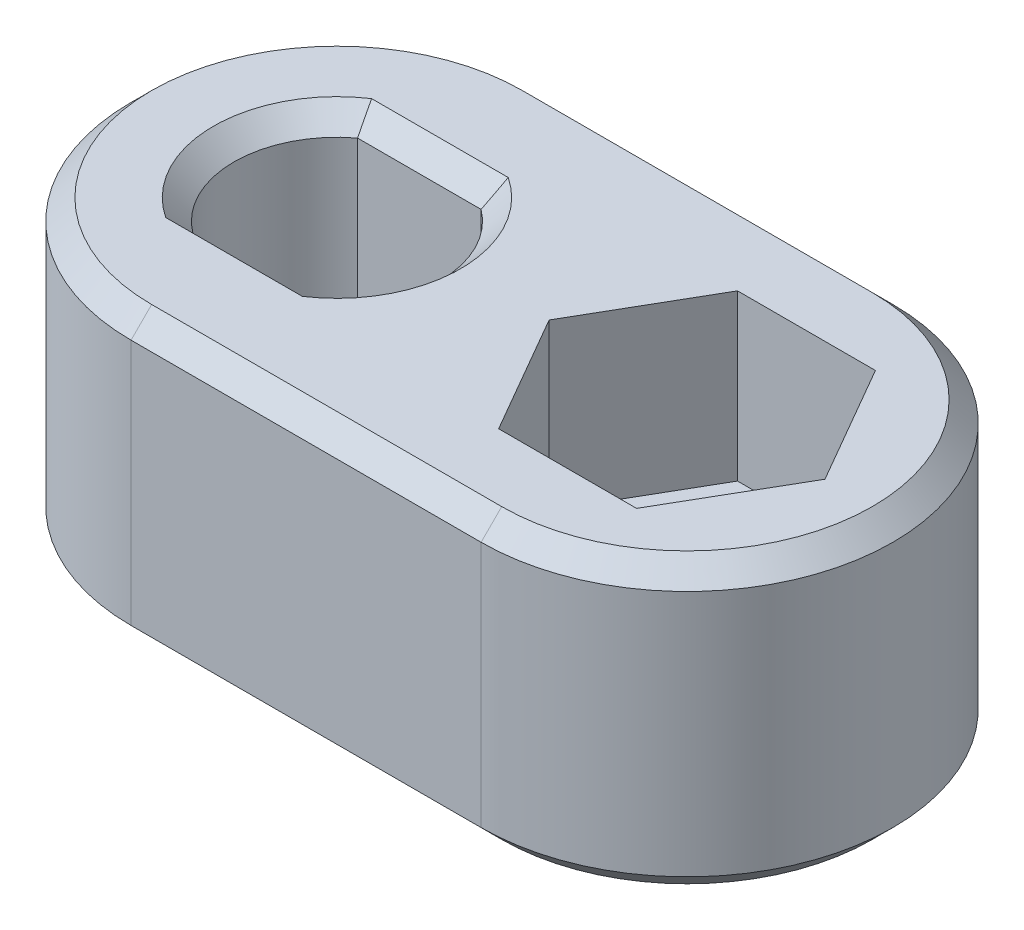
SolidWorks part; units mm, degrees
ref_plane "Front Plane" through (0, 0, 0) normal (0, 0, 1) x (1, 0, 0)
ref_plane "Top Plane" through (0, 0, 0) normal (0, 1, 0) x (1, 0, 0)
ref_plane "Right Plane" through (0, 0, 0) normal (1, 0, 0) x (0, 0, -1)
sketch "Sketch1" plane through (0, 0, 0) normal (0, 1, 0) x (1, 0, 0)
  line L0 (0, 0) -> (8.5, 0) construction
  line L1 (0, 5) -> (8.5, 5)
  line L2 (0, -5) -> (8.5, -5)
  arc A0 (0, 5) -> (0, -5) centre (0, 0) ccw
  arc A1 (8.5, -5) -> (8.5, 5) centre (8.5, 0) ccw
  point P3 (4.25, 0)
  dimension "D1" = 8.5
  dimension "D2" = 10
extrude "Boss-Extrude1" add sketch "Sketch1" along normal blind 7
sketch "Sketch2" plane through (0, 7, 0) normal (0, 1, 0) x (1, 0, 0)
  line L0 (-1.5, -2) -> (1.5, -2)
  line L1 (-1.5, 2) -> (1.5, 2)
  line L2 (0, 0) -> (-3.1448, 0) construction
  circle A0 centre (0, 0) radius 2.5
  dimension "D2" = 5
  dimension "D1" = 4
extrude "Cut-Extrude1" cut sketch "Sketch2" against normal blind 4
hole_wizard "CSK for M3 Hex Socket Countersunk Cap Screw2" positions "Sketch8" profile "Sketch7" countersink size "M3" standard "ISO"
sketch "Sketch8" plane through (0, 0, 0) normal (0, -1, 0) x (-1, 0, 0)
  point P0 (0, 0)
sketch "Sketch7" plane through (0, 0, 0) normal (1, 0, 0) x (0, 0, -1)
  line L0 (0, 0) -> (0, 8.5215)
  line L1 (0, 8.5215) -> (1.7, 7.5)
  line L2 (1.7, 7.5) -> (1.7, 1.66)
  line L3 (1.7, 1.66) -> (3.36, 0)
  line L5 (3.36, 0) -> (0, 0)
  line L6 (-1.7, 1.66) -> (-3.36, 0) construction
  line L10 (0, 8.5215) -> (-1.7, 7.5) construction
  line L11 (0, -6.35) -> (0, 107.95) construction
  dimension "Hole Dia." = 3.4
  dimension "Hole Depth" = 7.5
  dimension "Near C'Sink Dia." = 6.72
  dimension "Near C'Sink Angle" = 90
  dimension "Drill Angle" = 118
hole_wizard "Hole1" positions "Sketch9" profile "Sketch10" legacy end condition through all
sketch "Sketch9" plane through (0, 0, 0) normal (0, -1, 0) x (-1, 0, 0)
  point P0 (-8.5, 0)
sketch "Sketch10" plane through (8.5, 0, 0) normal (1, 0, 0) x (0, 0, -1)
  line L0 (0, 0) -> (0, 7)
  line L1 (0, 7) -> (2.075, 7)
  line L2 (2.075, 7) -> (2.075, 0)
  line L3 (2.075, 0) -> (0, 0)
  line L4 (0, 110) -> (0, -10) construction
  dimension "Diameter" = 4.15
  dimension "Depth" = 7
sketch "Sketch11" plane through (0, 7, 0) normal (0, 1, 0) x (1, 0, 0)
  line L0 (8.5, 5) -> (0, 5) construction
  line L1 (11.8486, 0) -> (10.1743, 2.9)
  line L2 (10.1743, 2.9) -> (6.8257, 2.9)
  line L3 (6.8257, 2.9) -> (5.1514, 0)
  line L4 (5.1514, 0) -> (6.8257, -2.9)
  line L5 (6.8257, -2.9) -> (10.1743, -2.9)
  line L6 (10.1743, -2.9) -> (11.8486, 0)
  circle A0 centre (8.5, 0) radius 2.9 construction
  dimension "D1" = 5.8
extrude "Cut-Extrude2" cut sketch "Sketch11" against normal blind 4
chamfer "Chamfer1" distance 0.5 angle 45 12 edges at (0, 7, -2) (-2.5, 7, 0) (2.5, 7, 0) (0, 7, 2) (-5, 7, 0) (4.25, 7, 5) (4.25, 7, -5) (13.5, 7, 0) (13.5, 0, 0) (4.25, 0, -5) (4.25, 0, 5) (-5, 0, 0)
